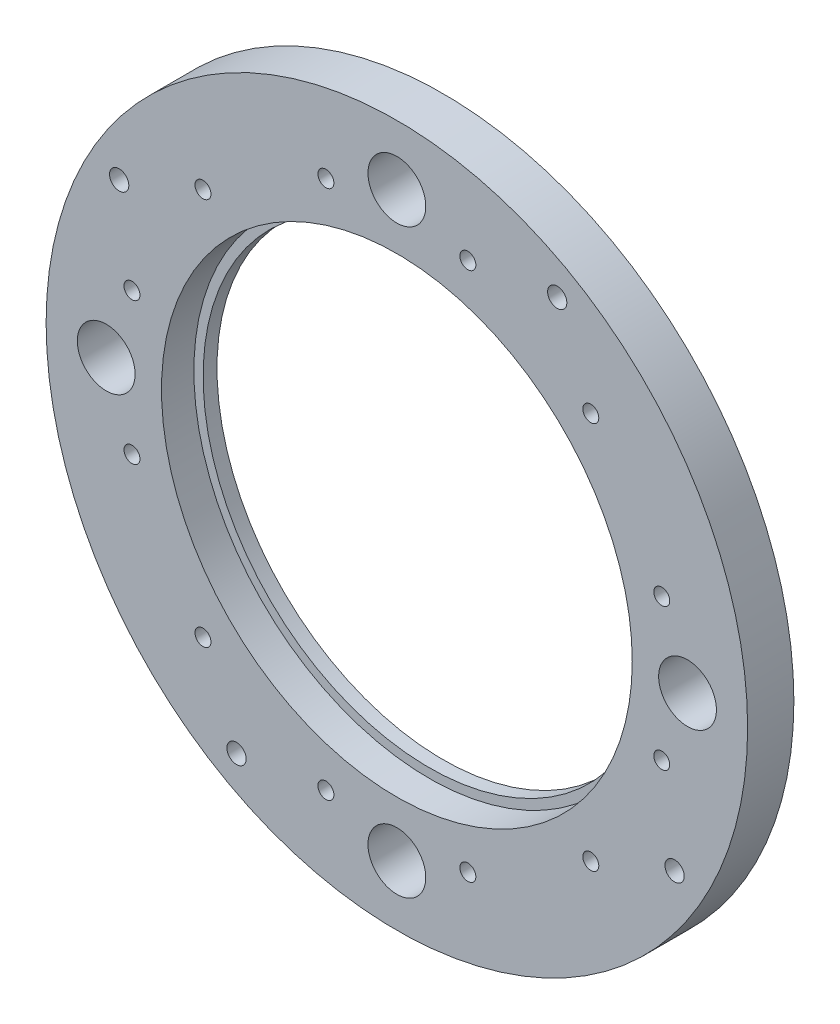
SolidWorks part; units mm, degrees
material "6061 Alloy"
ref_plane "Front Plane" through (0, 0, 0) normal (0, 0, 1) x (1, 0, 0)
ref_plane "Top Plane" through (0, 0, 0) normal (0, 1, 0) x (1, 0, 0)
ref_plane "Right Plane" through (0, 0, 0) normal (1, 0, 0) x (0, 0, -1)
ref_plane "Plane1" through (0, 0, 0) normal (0, -1, 0) x (1, 0, 0)
sketch "Sketch1" plane through (0, 0, 0) normal (0, -1, 0) x (1, 0, 0)
  line L0 (75.85, 5) -> (0, 5)
  line L1 (0, 5) -> (0, -5)
  line L2 (0, -5) -> (75.85, -5)
  line L3 (75.85, -5) -> (75.85, 5)
  line L4 (0, 5) -> (0, -5) construction
revolve "Revolve1" add sketch "Sketch1" angle 360 about L4
hole_wizard "M3.5 Clearance Hole1" positions "Sketch3" profile "Sketch2" hole size "M3.5" standard "ANSI Metric"
sketch "Sketch3" plane through (0, 0, -5) normal (0, 0, -1) x (-1, 0, 0)
  point P0 (60.0519, 34.671)
  point P1 (-34.671, 60.0519)
  point P2 (-60.0519, -34.671)
  point P3 (34.671, -60.0519)
sketch "Sketch2" plane through (-60.0519, 34.671, -5) normal (1, 0, 0) x (0, 1, 0)
  line L0 (0, 0) -> (0, 10)
  line L1 (0, 10) -> (2.0828, 10)
  line L2 (2.0828, 10) -> (2.0828, 0)
  line L5 (2.0828, 0) -> (0, 0)
  line L11 (0, -6.35) -> (0, 107.95) construction
  dimension "Thru Hole Dia." = 4.1656
  dimension "Thru Hole Depth" = 10
hole_wizard "M3 Clearance Hole1" positions "Sketch5" profile "Sketch4" hole size "M3" standard "ANSI Metric"
sketch "Sketch5" plane through (0, 0, -5) normal (0, 0, -1) x (-1, 0, 0)
  point P0 (41.9314, 41.9314)
  point P1 (57.2794, 15.348)
  point P2 (57.2794, -15.348)
  point P3 (41.9314, -41.9314)
  point P4 (15.348, -57.2794)
  point P5 (-15.348, -57.2794)
  point P6 (-41.9314, -41.9314)
  point P7 (-57.2794, -15.348)
  point P8 (-57.2794, 15.348)
  point P9 (-41.9314, 41.9314)
  point P10 (-15.348, 57.2794)
  point P11 (15.348, 57.2794)
sketch "Sketch4" plane through (-41.9314, 41.9314, -5) normal (1, 0, 0) x (0, 1, 0)
  line L0 (0, 0) -> (0, 10)
  line L1 (0, 10) -> (1.7272, 10)
  line L2 (1.7272, 10) -> (1.7272, 0)
  line L5 (1.7272, 0) -> (0, 0)
  line L11 (0, -6.35) -> (0, 107.95) construction
  dimension "Thru Hole Dia." = 3.4544
  dimension "Thru Hole Depth" = 10
hole_wizard "Ø12.5 (12.5) Diameter Hole1" positions "Sketch7" profile "Sketch6" hole size "Ø12.5" standard "ANSI Metric"
sketch "Sketch7" plane through (0, 0, -5) normal (0, 0, -1) x (-1, 0, 0)
  point P0 (62.85, 0)
  point P1 (0, -62.85)
  point P2 (-62.85, 0)
  point P3 (0, 62.85)
sketch "Sketch6" plane through (-62.85, 0, -5) normal (1, 0, 0) x (0, 1, 0)
  line L0 (0, 0) -> (0, 10)
  line L1 (0, 10) -> (6.25, 10)
  line L2 (6.25, 10) -> (6.25, 0)
  line L5 (6.25, 0) -> (0, 0)
  line L11 (0, -6.35) -> (0, 107.95) construction
  dimension "Thru Hole Dia." = 12.5
  dimension "Thru Hole Depth" = 10
hole_wizard "CBORE for M90 Hex Head Bolt1" positions "Sketch9" profile "Sketch8" counterbore size "M90" standard "ANSI Metric"
sketch "Sketch9" plane through (0, 0, 5) normal (0, 0, 1) x (1, 0, 0)
  point P0 (0, 0)
sketch "Sketch8" plane through (0, 0, 5) normal (1, 0, 0) x (0, -1, 0)
  line L0 (0, 0) -> (0, 10)
  line L1 (0, 10) -> (48.9, 10)
  line L3 (48.9, 10) -> (48.9, 7)
  line L4 (48.9, 7) -> (50.9, 7)
  line L5 (50.9, 7) -> (50.9, 0)
  line L7 (50.9, 0) -> (0, 0)
  line L11 (0, -6.35) -> (0, 107.95) construction
  dimension "Thru Hole Dia." = 97.8
  dimension "Thru Hole Depth" = 10
  dimension "C'Bore Dia." = 101.8
  dimension "C'Bore Depth" = 7
sketch "Sketch10" plane through (0, 0, -5) normal (0, 0, -1) x (-1, 0, 0)
  line L0 (0, 62.85) -> (0, -62.85) construction
  line L1 (0, 0) -> (57.2794, -15.348) construction
  line L2 (0, 0) -> (-62.85, 0) construction
  line L3 (0, 0) -> (-60.0519, -34.671) construction
  line L4 (0, 0) -> (34.671, -60.0519) construction
  line L5 (0, 0) -> (57.2794, 15.348) construction
